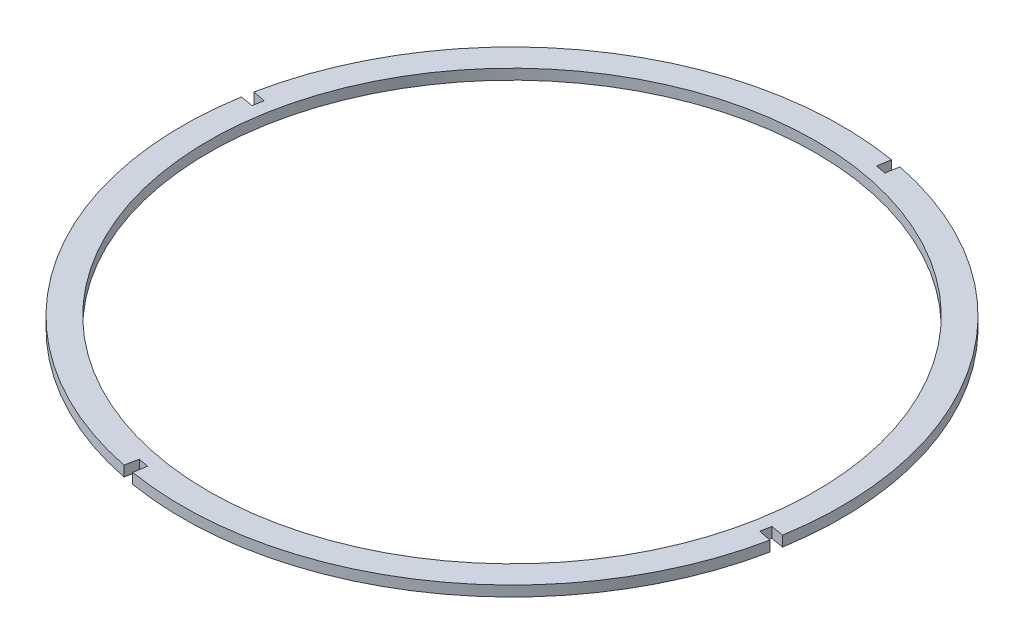
SolidWorks part; units mm, degrees
ref_plane "Спереди" through (0, 0, 0) normal (0, 0, 1) x (1, 0, 0)
ref_plane "Сверху" through (0, 0, 0) normal (0, 1, 0) x (1, 0, 0)
ref_plane "Справа" through (0, 0, 0) normal (1, 0, 0) x (0, 0, -1)
other "Configuration Table"
sketch "Эскиз1" plane through (0, 0, 0) normal (0, 1, 0) x (1, 0, 0)
  line L0 (-322.9779, 653.4345) -> (-307.2434, 650.5318)
  line L1 (-403.4657, 173.0347) -> (-315.1107, 651.9831) construction
  line L3 (-322.9779, 653.4345) -> (-319.684, 673.0947)
  line L4 (-307.2434, 650.5318) -> (-303.6266, 670.1379)
  line L6 (-315.1107, 651.9831) -> (-491.5437, -305.9648) construction
  line L7 (-403.4657, 173.0347) -> (75.4828, 84.6797) construction
  line L8 (-403.4657, 173.0347) -> (-882.4141, 261.3896) construction
  line L9 (76.9341, 92.547) -> (74.0315, 76.8125)
  line L10 (74.0315, 76.8125) -> (93.573, 72.8746)
  line L11 (76.9341, 92.547) -> (96.5944, 89.253)
  line L12 (-499.4114, -304.5158) -> (-483.676, -307.4139)
  line L13 (-499.4114, -304.5158) -> (-503.3384, -324.0618)
  line L14 (-483.676, -307.4139) -> (-486.9582, -327.0737)
  line L15 (-880.9628, 269.2569) -> (-883.8654, 253.5224)
  line L16 (-880.9628, 269.2569) -> (-900.5688, 272.8737)
  line L17 (-883.8654, 253.5224) -> (-903.5257, 256.8163)
  arc A0 (-319.684, 673.0947) -> (-900.5688, 272.8737) centre (-403.4657, 173.0347) ccw
  circle A1 centre (-403.4657, 173.0347) radius 467.03
  arc A2 (96.5944, 89.253) -> (-303.6266, 670.1379) centre (-403.4657, 173.0347) ccw
  arc A3 (-486.9582, -327.0737) -> (93.573, 72.8746) centre (-403.4657, 173.0347) ccw
  arc A4 (-903.5257, 256.8163) -> (-503.3384, -324.0618) centre (-403.4657, 173.0347) ccw
  point P7 (-315.1107, 651.9831)
  point P13 (-491.5437, -305.9648)
  point P16 (75.4828, 84.6797)
  point P24 (-882.4141, 261.3896)
  dimension "D1" = 1014.06
  dimension "D2" = 934.06
  dimension "D3" = 0
  dimension "D4" = 0
  dimension "D5" = 16
  dimension "D6" = 16
  dimension "D7" = 0
  dimension "D8" = 487.03
  dimension "D9" = 16
  dimension "D10" = 0
  dimension "D11" = 16
  dimension "D12" = 0
  dimension "D13" = 487.03
  dimension "D14" = 487.03
  dimension "D15" = 487.03
  dimension "D16" = 0
sketch "Эскиз4" plane through (0, 0, 0) normal (0, 1, 0) x (1, 0, 0)
extrude "Бобышка-Вытянуть4" add sketch "Эскиз1" along normal blind 16
